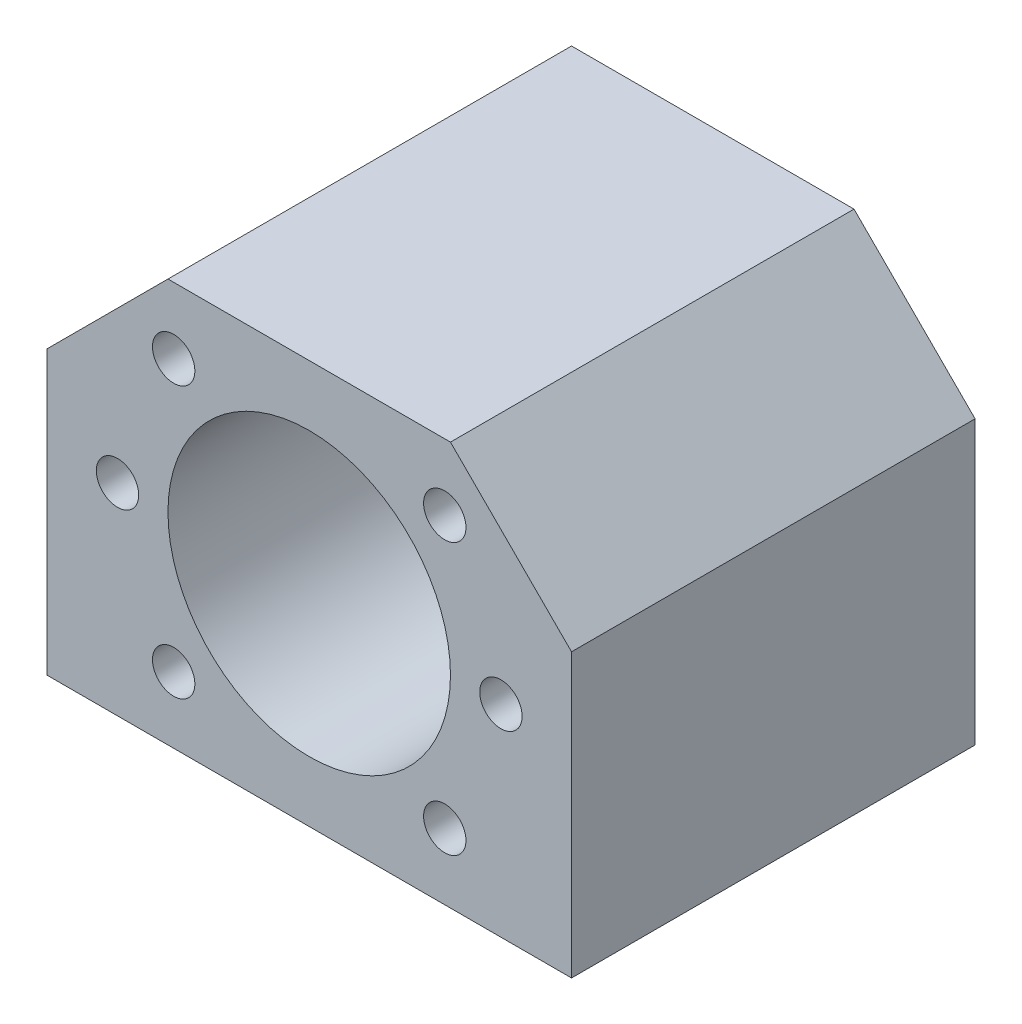
SolidWorks part; units mm, degrees
material "6061 Alloy"
ref_plane "Front Plane" through (0, 0, 0) normal (0, 0, 1) x (1, 0, 0)
ref_plane "Top Plane" through (0, 0, 0) normal (0, 1, 0) x (1, 0, 0)
ref_plane "Right Plane" through (0, 0, 0) normal (1, 0, 0) x (0, 0, -1)
sketch "Sketch1" plane through (0, 0, 0) normal (0, 0, 1) x (1, 0, 0)
  line L0 (-26, 8) -> (-14, 20)
  line L1 (26, -20) -> (-26, -20)
  line L2 (26, -20) -> (26, 20)
  line L3 (26, 20) -> (-26, 20)
  line L4 (-26, -20) -> (-26, 20)
  line L5 (26, -20) -> (-26, 20) construction
  line L6 (26, 20) -> (-26, -20) construction
  line L7 (14, 20) -> (26, 8)
  circle A0 centre (0, 0) radius 14
  dimension "D1" = 28
  dimension "D2" = 40
  dimension "D3" = 52
  dimension "D4" = 12
  dimension "D5" = 12
  dimension "D6" = 12
  dimension "D7" = 12
extrude "Boss-Extrude1" add sketch "Sketch1" along normal mid plane 40 contours L7 L3 L0 L4 L1 L2 A0
hole_wizard "M5x0.8 Tapped Hole1" positions "Sketch2" profile "Sketch4" tap size "M5x0.8" standard "ANSI Metric"
sketch "Sketch2" plane through (0, 0, 20) normal (0, 0, 1) x (1, 0, 0)
  line L0 (13.435, -13.435) -> (-13.435, 13.435) construction
  line L2 (-13.435, -13.435) -> (13.435, 13.435) construction
  circle A0 centre (0, 0) radius 19 construction
  point P6 (19, 0)
  point P8 (-19, 0)
  point P13 (-13.435, 13.435)
  point P45 (13.435, -13.435)
  point P46 (0, 0)
  point P50 (13.435, 13.435)
  point P85 (-13.435, -13.435)
  point P86 (0, 0)
  dimension "D1" = 38
  dimension "D2" = 45
  dimension "D3" = 90
sketch "Sketch4" plane through (0, 0, 20) normal (1, 0, 0) x (0, -1, 0)
  line L0 (0, 0) -> (0, 13.4538)
  line L1 (0, 13.4538) -> (2.1, 12.192)
  line L2 (2.1, 12.192) -> (2.1, 0)
  line L5 (2.1, 0) -> (0, 0)
  line L10 (0, 13.4538) -> (-2.1, 12.192) construction
  line L11 (0, -6.35) -> (0, 107.95) construction
  dimension "Tap Drill Dia." = 4.2
  dimension "Tap Drill Depth" = 12.192
  dimension "Drill Angle" = 118
cosmetic thread "Hole Thread1" parameters "D1"=9.906, "D2"=5
cosmetic thread "Hole Thread2" parameters "D1"=9.906, "D2"=5
cosmetic thread "Hole Thread3" parameters "D1"=9.906, "D2"=5
cosmetic thread "Hole Thread4" parameters "D1"=9.906, "D2"=5
cosmetic thread "Hole Thread5" parameters "D1"=9.906, "D2"=5
cosmetic thread "Hole Thread6" parameters "D1"=9.906, "D2"=5
hole_wizard "M5x0.8 Tapped Hole2" positions "Sketch5" profile "Sketch6" tap size "M5x0.8" standard "ANSI Metric"
sketch "Sketch5" plane through (0, -20, 0) normal (0, -1, 0) x (-1, 0, 0)
  point P0 (20, -12)
  point P2 (-20, -12)
  point P4 (-20, 12)
  point P6 (20, 12)
  dimension "D1" = 40
  dimension "D2" = 24
  dimension "D3" = 12
  dimension "D4" = 20
sketch "Sketch6" plane through (-20, -20, 12) normal (1, 0, 0) x (0, 0, -1)
  line L0 (0, 0) -> (0, 13.4538)
  line L1 (0, 13.4538) -> (2.1, 12.192)
  line L2 (2.1, 12.192) -> (2.1, 0)
  line L5 (2.1, 0) -> (0, 0)
  line L10 (0, 13.4538) -> (-2.1, 12.192) construction
  line L11 (0, -6.35) -> (0, 107.95) construction
  dimension "Tap Drill Dia." = 4.2
  dimension "Tap Drill Depth" = 12.192
  dimension "Drill Angle" = 118
cosmetic thread "Hole Thread7" parameters "D1"=9.906, "D2"=5
cosmetic thread "Hole Thread8" parameters "D1"=9.906, "D2"=5
cosmetic thread "Hole Thread9" parameters "D1"=9.906, "D2"=5
cosmetic thread "Hole Thread10" parameters "D1"=9.906, "D2"=5
equation "\"D3@Sketch5\"=\"D2@Sketch5\"/2"
equation "\"D4@Sketch5\"=\"D1@Sketch5\"/2"
